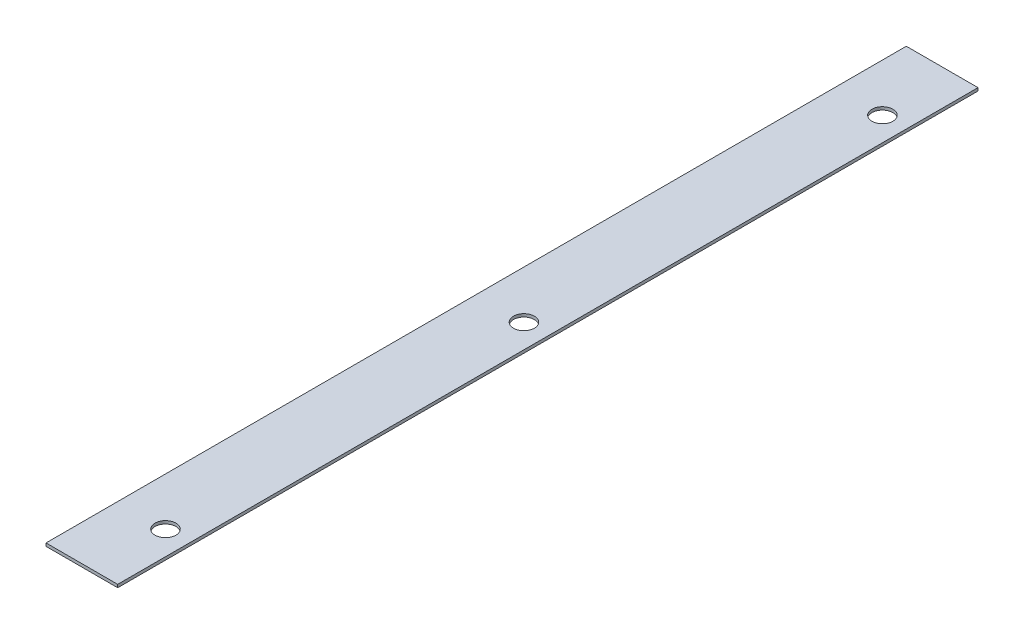
SolidWorks part; units mm, degrees
ref_plane "Front Plane" through (0, 0, 0) normal (0, 0, 1) x (1, 0, 0)
ref_plane "Top Plane" through (0, 0, 0) normal (0, 1, 0) x (1, 0, 0)
ref_plane "Right Plane" through (0, 0, 0) normal (1, 0, 0) x (0, 0, -1)
sketch "Sketch1" plane through (0, 0, 0) normal (0, 1, 0) x (1, 0, 0)
  line L1 (0, 0) -> (76.2, 0)
  line L2 (0, 0) -> (0, 914.4)
  line L3 (0, 914.4) -> (76.2, 914.4)
  line L4 (76.2, 0) -> (76.2, 914.4)
  dimension "D1" = 914.4
  dimension "D2" = 76.2
extrude "Boss-Extrude1" add sketch "Sketch1" along normal blind 3.175
sketch "Sketch2" plane through (0, 3.175, 0) normal (0, 1, 0) x (1, 0, 0)
  line L0 (76.2, 457.2) -> (0, 457.2) construction
  line L2 (76.2, 0) -> (76.2, 914.4) construction
  line L3 (0, 914.4) -> (0, 0) construction
  line L4 (50.8, 914.4) -> (50.8, 0) construction
  line L5 (76.2, 914.4) -> (0, 914.4) construction
  line L6 (0, 0) -> (76.2, 0) construction
  circle A0 centre (50.8, 838.2) radius 11.1125
  circle A1 centre (50.8, 457.2) radius 11.1125
  circle A2 centre (50.8, 76.2) radius 11.1125
  dimension "D2" = 22.225
  dimension "D1" = 25.4
  dimension "D3" = 76.2
extrude "Cut-Extrude1" cut sketch "Sketch2" against normal up to next
